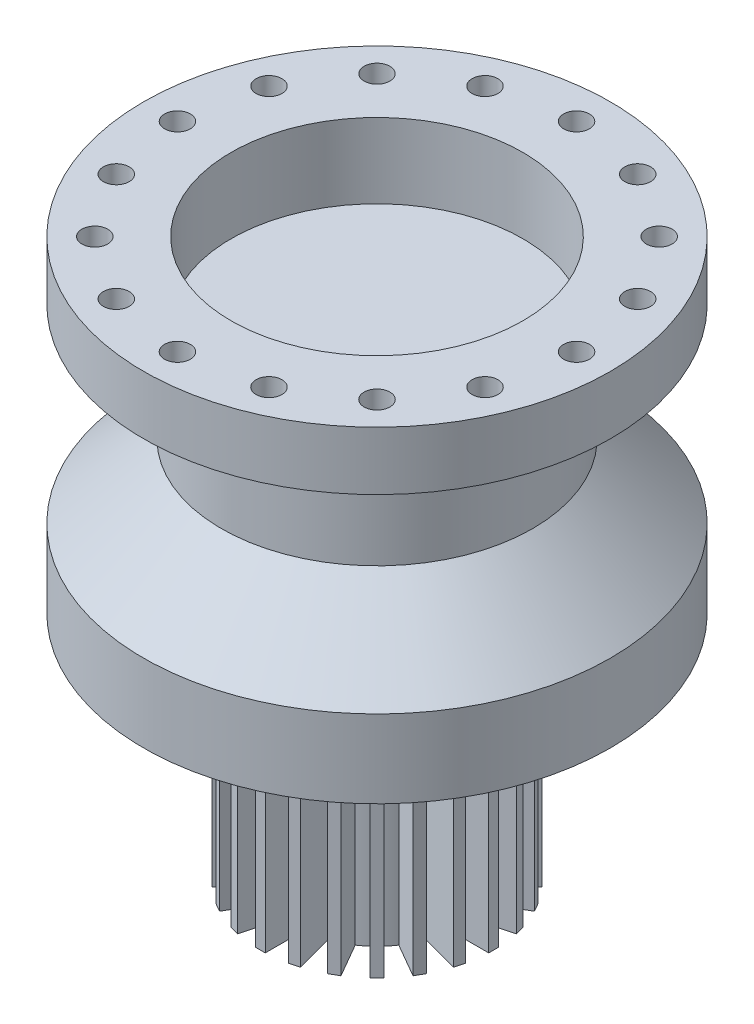
SolidWorks part; units mm, degrees
material "6061-T6 (SS)"
ref_plane "Front Plane" through (0, 0, 0) normal (0, 0, 1) x (1, 0, 0)
ref_plane "Top Plane" through (0, 0, 0) normal (0, 1, 0) x (1, 0, 0)
ref_plane "Right Plane" through (0, 0, 0) normal (1, 0, 0) x (0, 0, -1)
sketch "Sketch1" plane through (0, 0, 0) normal (0, 0, 1) x (1, 0, 0)
  line L0 (0, -1509.7597) -> (0, 73978.2236) construction
  line L1 (47.625, 0) -> (76.2, 0)
  line L2 (76.2, 0) -> (76.2, -19.05)
  line L3 (76.2, -19.05) -> (50.8, -19.05)
  line L4 (50.8, -19.05) -> (50.8, -57.15)
  line L5 (50.8, -57.15) -> (76.2, -81.0531)
  line L6 (76.2, -81.0531) -> (76.2, -106.4531)
  line L7 (76.2, -106.4531) -> (25.4, -106.4531)
  line L8 (25.4, -106.4531) -> (25.4, -182.6531)
  line L9 (25.4, -182.6531) -> (0, -182.6531)
  line L10 (0, -182.6531) -> (0, -24.4023)
  line L11 (0, -24.4023) -> (47.625, -24.4023)
  line L12 (47.625, -24.4023) -> (47.625, 0)
  dimension "D1" = 152.4
  dimension "D2" = 19.05
  dimension "D4" = 38.1
  dimension "D5" = 101.6
  dimension "D6" = 25.4
  dimension "D7" = 76.2
  dimension "D8" = 50.8
  dimension "D9" = 3.175
revolve "Revolve1" add sketch "Sketch1" angle 360 about L0
sketch "Sketch2" plane through (0, -106.4531, 0) normal (0, -1, 0) x (1, 0, 0)
  line L1 (-1.5875, 25.3503) -> (1.5875, 25.3503)
  line L2 (-1.5875, 25.3503) -> (-1.5875, 38.0503)
  line L3 (-1.5875, 38.0503) -> (1.5875, 38.0503)
  line L4 (1.5875, 25.3503) -> (1.5875, 38.0503)
  circle A0 centre (0, 0) radius 25.4 construction
  circle A1 centre (0, 0) radius 25.4 construction
  dimension "D1" = 12.7
  dimension "D2" = 3.175
extrude "Boss-Extrude1" add sketch "Sketch2" along normal up to surface (76.2 mm away) up to face at (25.4, -182.6531, 0)
pattern_circular "CirPattern1" count 24 over 360 about axis through (0, 0, 0) along (0, 1, 0) of "Boss-Extrude1"
hole_wizard "5/16 Clearance Hole1" positions "Sketch3" profile "Sketch4" hole size "5/16" standard "ANSI Inch" end condition up to next
sketch "Sketch3" plane through (0, 0, 0) normal (0, 1, 0) x (1, 0, 0)
  circle A0 centre (0, 0) radius 65.1256
  point P0 (0, 65.1256)
  dimension "D1" = 130.2512
sketch "Sketch4" plane through (0, 0, -65.1256) normal (1, 0, 0) x (0, 0, 1)
  line L0 (0, 0) -> (0, 19.05)
  line L1 (0, 19.05) -> (4.2164, 19.05)
  line L2 (4.2164, 19.05) -> (4.2164, 0)
  line L5 (4.2164, 0) -> (0, 0)
  line L11 (0, -6.35) -> (0, 107.95) construction
  dimension "Thru Hole Dia." = 8.4328
  dimension "Thru Hole Depth" = 19.05
pattern_circular "CirPattern2" count 16 over 360 about axis through (0, 0, 0) along (0, 1, 0) of "5/16 Clearance Hole1"
